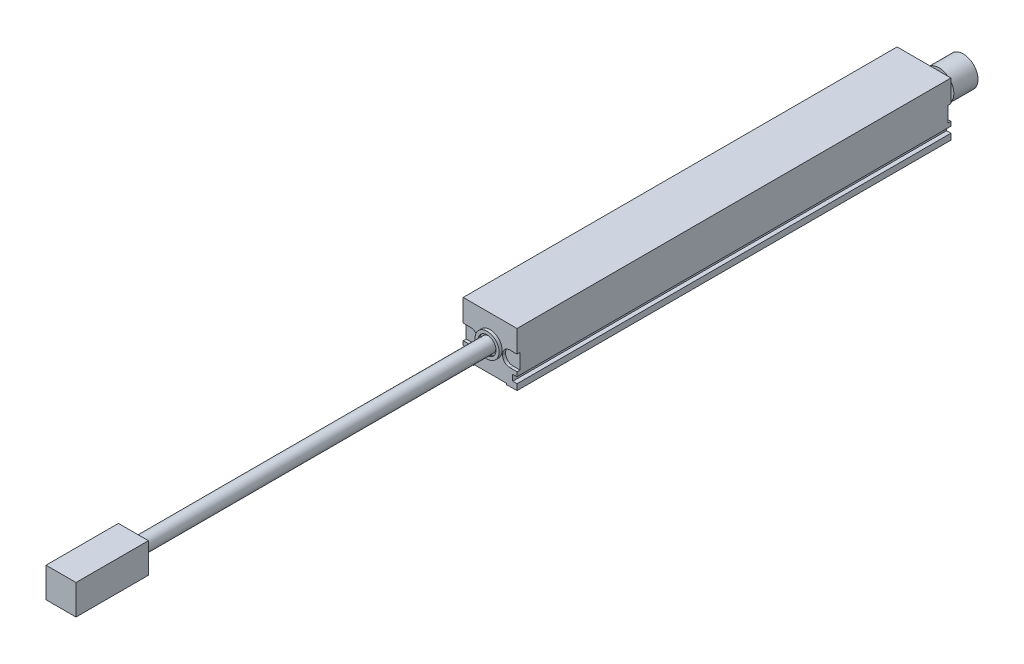
SolidWorks part; units mm, degrees
ref_plane "Alzado" through (0, 0, 0) normal (0, 0, 1) x (1, 0, 0)
ref_plane "Planta" through (0, 0, 0) normal (0, 1, 0) x (1, 0, 0)
ref_plane "Vista lateral" through (0, 0, 0) normal (1, 0, 0) x (0, 0, -1)
sketch "Croquis1" plane through (0, 0, 0) normal (0, 0, 1) x (1, 0, 0)
  line L1 (0, 0) -> (17.8, 0)
  line L2 (0, 0) -> (0, 17.82)
  line L3 (0, 17.82) -> (17.8, 17.82)
  line L4 (17.8, 0) -> (17.8, 17.82)
  dimension "D1" = 17.8
  dimension "D2" = 17.82
extrude "Saliente-Extruir1" add sketch "Croquis1" along normal blind 143.52
sketch "Croquis2" plane through (0, 0, 0) normal (0, -1, 0) x (1, 0, 0)
  line L0 (3.4, 143.52) -> (14.4, 143.52)
  line L1 (0, 143.52) -> (17.8, 143.52) construction
  line L2 (3.4, 143.52) -> (3.4, 0)
  line L3 (0, 0) -> (17.8, 0) construction
  line L4 (3.4, 0) -> (14.4, 0)
  line L5 (14.4, 0) -> (14.4, 143.52)
  point P7 (8.9, 143.52)
  dimension "D1" = 11
extrude "Cortar-Extruir1" cut sketch "Croquis2" against normal blind 0.38
sketch "Croquis3" plane through (0, 0, 0) normal (0, 0, -1) x (-1, 0, 0)
  line L0 (0, 0) -> (0, 2) construction
  line L1 (0, 17.82) -> (0, 0) construction
  line L2 (0, 2) -> (-17.8, 2)
  line L3 (-17.8, 0) -> (-17.8, 17.82) construction
  line L4 (-17.8, 2) -> (-17.8, 4)
  line L5 (0, 2) -> (0, 4)
  line L6 (-1.42, 4) -> (-1.42, 2)
  line L7 (-1.42, 4) -> (0, 4)
  line L8 (-17.8, 4) -> (-16.38, 4)
  line L9 (-16.38, 4) -> (-16.38, 2)
  line M13 (0, 0) -> (0, 17.82)
  line M15 (-17.8, 17.82) -> (-17.8, 0)
  dimension "D1" = 2
  dimension "D2" = 2
  dimension "D3" = 1.42
  dimension "D4" = 1.42
extrude "Cortar-Extruir2" cut sketch "Croquis3" against normal through all contours L9 L8 L2 M15 | L7 L6 L2 M13
sketch "Croquis4" plane through (0, 0, 0) normal (0, 0, -1) x (-1, 0, 0)
  line L0 (0, 17.82) -> (0, 10.47) construction
  line L1 (0, 17.82) -> (0, 4) construction
  line L2 (0, 0) -> (0, 5.42) construction
  line L3 (0, 5.42) -> (-4.77, 5.42)
  line L4 (-4.77, 5.42) -> (-4.77, 10.47)
  line L5 (-4.77, 10.47) -> (0, 10.47)
  line L6 (0, 10.47) -> (0, 5.42)
  line L7 (-17.8, 10.47) -> (-13.03, 10.47)
  line L8 (-17.8, 4) -> (-17.8, 17.82) construction
  line L9 (-13.03, 10.47) -> (-13.03, 5.42)
  line L10 (-13.03, 5.42) -> (-17.8, 5.42)
  line L11 (-17.8, 10.47) -> (-17.8, 5.42)
  dimension "D1" = 7.35
  dimension "D2" = 5.42
  dimension "D3" = 4.77
  dimension "D4" = 4.77
extrude "Cortar-Extruir3" cut sketch "Croquis4" against normal blind 1
sketch "Croquis5" plane through (0, 0, 1) normal (0, 0, -1) x (-1, 0, 0)
  line L0 (-17.8, 10.47) -> (-13.03, 10.47)
  line L1 (-13.03, 10.47) -> (-13.03, 5.42)
  line L2 (-13.03, 5.42) -> (-17.8, 5.42)
  line L3 (-17.8, 5.42) -> (-17.8, 10.47)
  line L4 (0, 10.47) -> (-4.77, 10.47)
  line L5 (-4.77, 10.47) -> (-4.77, 5.42)
  line L6 (-4.77, 5.42) -> (0, 5.42)
  line L7 (0, 5.42) -> (0, 10.47)
extrude "Cortar-Extruir4" cut sketch "Croquis5" along normal blind 1 from surface at -142.52 contours L7 L4 L5 L6 | L3 L0 L1 L2 starting at face at (8.9, 3.775, 143.52)
fillet "Redondeo1" radius 2.385 1 edges at (4.77, 5.42, 0.5)
fillet "Redondeo2" radius 2.385 1 edges at (4.77, 10.47, 0.5)
fillet "Redondeo3" radius 2.385 1 edges at (13.03, 10.47, 0.5)
fillet "Redondeo4" radius 2.385 1 edges at (13.03, 5.42, 0.5)
fillet "Redondeo5" radius 2.385 1 edges at (13.03, 10.47, 143.02)
fillet "Redondeo6" radius 2.385 1 edges at (13.03, 5.42, 143.02)
fillet "Redondeo7" radius 2.385 1 edges at (4.77, 5.42, 143.02)
fillet "Redondeo8" radius 2.385 1 edges at (4.77, 10.47, 143.02)
sketch "Croquis6" plane through (0, 0, 143.52) normal (0, 0, 1) x (1, 0, 0)
  line L0 (0, 17.82) -> (17.8, 17.82) construction
  line L1 (8.9, 17.82) -> (8.9, 0.38) construction
  line L2 (14.4, 0.38) -> (3.4, 0.38) construction
  circle A0 centre (8.9, 9.1) radius 3.975
  dimension "D1" = 7.95
extrude "Saliente-Extruir2" add sketch "Croquis6" along normal blind 1
sketch "Croquis7" plane through (0, 0, 144.52) normal (0, 0, 1) x (1, 0, 0)
  circle A0 centre (8.9, 9.1) radius 2.95
  dimension "D1" = 5.9
extrude "Cortar-Extruir5" cut sketch "Croquis7" against normal blind 0.5
sketch "Croquis8" plane through (0, 0, 144.02) normal (0, 0, 1) x (1, 0, 0)
  circle A0 centre (8.9, 9.1) radius 2.4
  dimension "D1" = 4.8
extrude "Saliente-Extruir3" add sketch "Croquis8" along normal blind 117.49
sketch "Croquis9" plane through (0, 0, 261.51) normal (0, 0, 1) x (1, 0, 0)
  line L0 (8.9, 4.145) -> (8.9, 14.055)
  line L1 (3.94, 14.055) -> (13.86, 14.055)
  line L2 (13.86, 14.055) -> (13.86, 4.145)
  line L3 (13.86, 4.145) -> (3.94, 4.145)
  line L4 (3.94, 4.145) -> (3.94, 14.055)
  point P5 (8.9, 9.1)
  point P6 (8.9, 14.055)
  circle M2 centre (8.9, 9.1) radius 2.4
  dimension "D1" = 4.955
  dimension "D2" = 4.96
extrude "Saliente-Extruir4" add sketch "Croquis9" along normal blind 23.95 contours L4 L3 L0 L1 M2 | L3 L2 L1 L0 M2 | L0 M2 | L0 M2
sketch "Croquis10" plane through (0, 0, 0) normal (0, 0, -1) x (-1, 0, 0)
  line L0 (0, 0) -> (-4.77, 0) construction
  line L1 (-4.77, 0) -> (-4.77, 17.82) construction
  line L2 (-17.8, 17.82) -> (0, 17.82) construction
  line L3 (-4.77, 8.91) -> (-8.135, 8.91) construction
  line L4 (-17.8, 8.91) -> (0, 8.91) construction
  line L5 (-17.8, 10.47) -> (-17.8, 5.42) construction
  line L6 (0, 5.42) -> (0, 10.47) construction
  circle A0 centre (-8.9, 8.91) radius 3.185
  dimension "D2" = 6.37
  dimension "D1" = 4.77
extrude "Saliente-Extruir5" add sketch "Croquis10" along normal blind 4.95
sketch "Croquis14" plane through (0, 0, 0) normal (0, 0, -1) x (-1, 0, 0)
  line L0 (-17.8, 17.82) -> (0, 17.82) construction
  line L1 (0, 17.82) -> (-8.9, 17.82) construction
  line L2 (-8.9, 17.82) -> (-8.9, 0) construction
  line L3 (-8.9, 0) -> (-8.9, 8.91) construction
  point P7 (-12.806, 10.7137)
  point P8 (-9.9698, 5.4394)
sketch "Croquis15" plane through (0, 0, -4.95) normal (0, 0, -1) x (-1, 0, 0)
  circle A0 centre (-8.9, 8.91) radius 4.92
  dimension "D1" = 9.84
extrude "Saliente-Extruir6" add sketch "Croquis15" along normal blind 8
